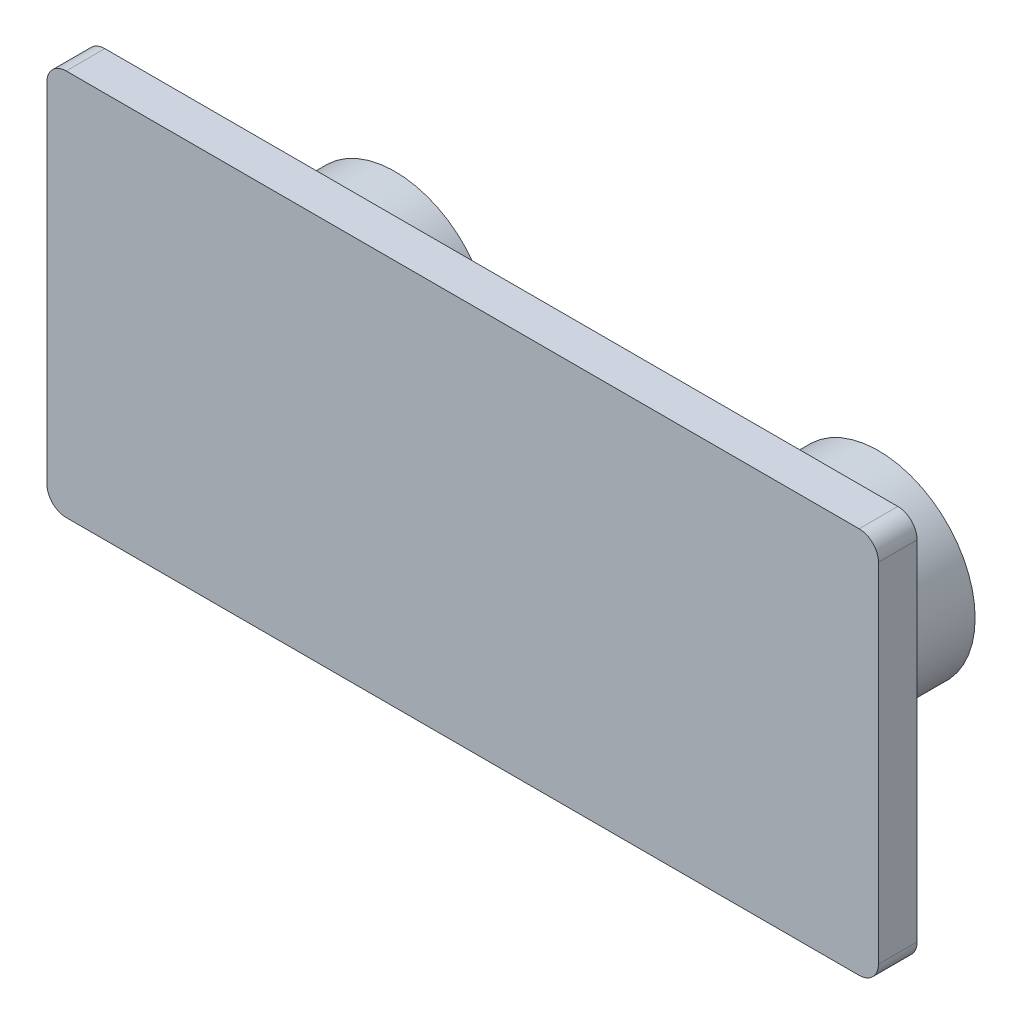
SolidWorks part; units mm, degrees
ref_plane "Front Plane" through (0, 0, 0) normal (0, 0, 1) x (1, 0, 0)
ref_plane "Top Plane" through (0, 0, 0) normal (0, 1, 0) x (1, 0, 0)
ref_plane "Right Plane" through (0, 0, 0) normal (1, 0, 0) x (0, 0, -1)
sketch "Sketch1" plane through (0, 0, 0) normal (0, 0, 1) x (1, 0, 0)
  line L1 (-21.5, -10) -> (21.5, -10)
  line L2 (-21.5, -10) -> (-21.5, 10)
  line L3 (-21.5, 10) -> (21.5, 10)
  line L4 (21.5, -10) -> (21.5, 10)
  line L5 (-21.5, -10) -> (21.5, 10) construction
  line L6 (-21.5, 10) -> (21.5, -10) construction
  point P0 (0, 0)
  dimension "D1" = 43
  dimension "D2" = 20
extrude "Boss-Extrude1" add sketch "Sketch1" along normal mid plane 2
sketch "Sketch2" plane through (0, 0, -1) normal (0, 0, 1) x (1, 0, 0)
  line L0 (-12.5, 0) -> (12.5, 0) construction
  circle A0 centre (-12.5, 0) radius 5
  circle A1 centre (12.5, 0) radius 5
  point P4 (0, 0)
  dimension "D2" = 10
  dimension "D1" = 25
extrude "Boss-Extrude2" add sketch "Sketch2" against normal blind 7
fillet "Fillet1" radius 2 2 edges at (-17.5, 0, -1) (7.5, 0, -1)
fillet "Fillet2" radius 1 4 edges at (21.5, 10, 0) (21.5, -10, 0) (-21.5, -10, 0) (-21.5, 10, 0)
